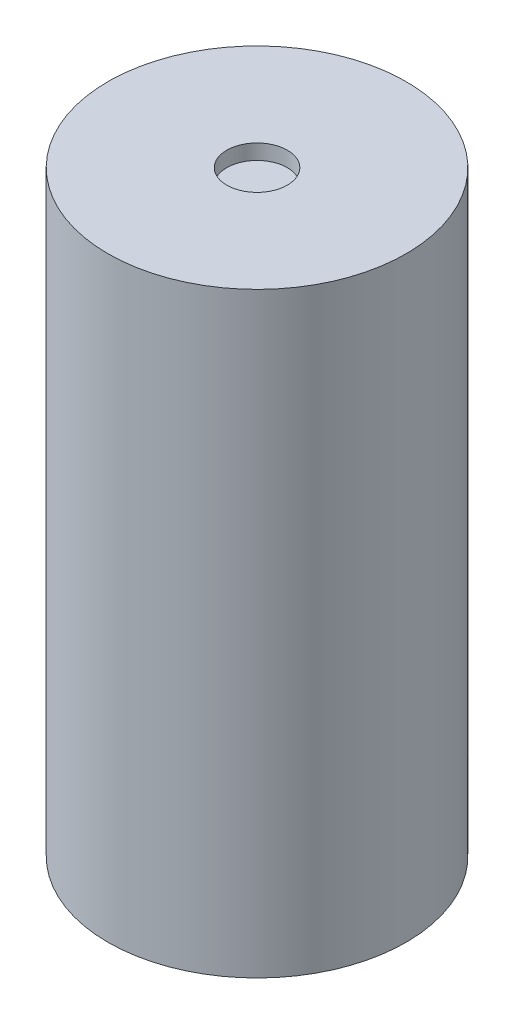
SolidWorks part; units mm, degrees
ref_plane "Front Plane" through (0, 0, 0) normal (0, 0, 1) x (1, 0, 0)
ref_plane "Top Plane" through (0, 0, 0) normal (0, 1, 0) x (1, 0, 0)
ref_plane "Right Plane" through (0, 0, 0) normal (1, 0, 0) x (0, 0, -1)
sketch "Sketch1" plane through (0, 0, 0) normal (0, 1, 0) x (1, 0, 0)
  circle A0 centre (0, 0) radius 250
  dimension "D1" = 500
extrude "Boss-Extrude1" add sketch "Sketch1" along normal blind 1000
sketch "Sketch2" plane through (0, 1000, 0) normal (0, 1, 0) x (1, 0, 0)
  circle A0 centre (0, 0) radius 50.8
  dimension "D1" = 101.6
extrude "Cut-Extrude1" cut sketch "Sketch2" against normal blind 25.4
